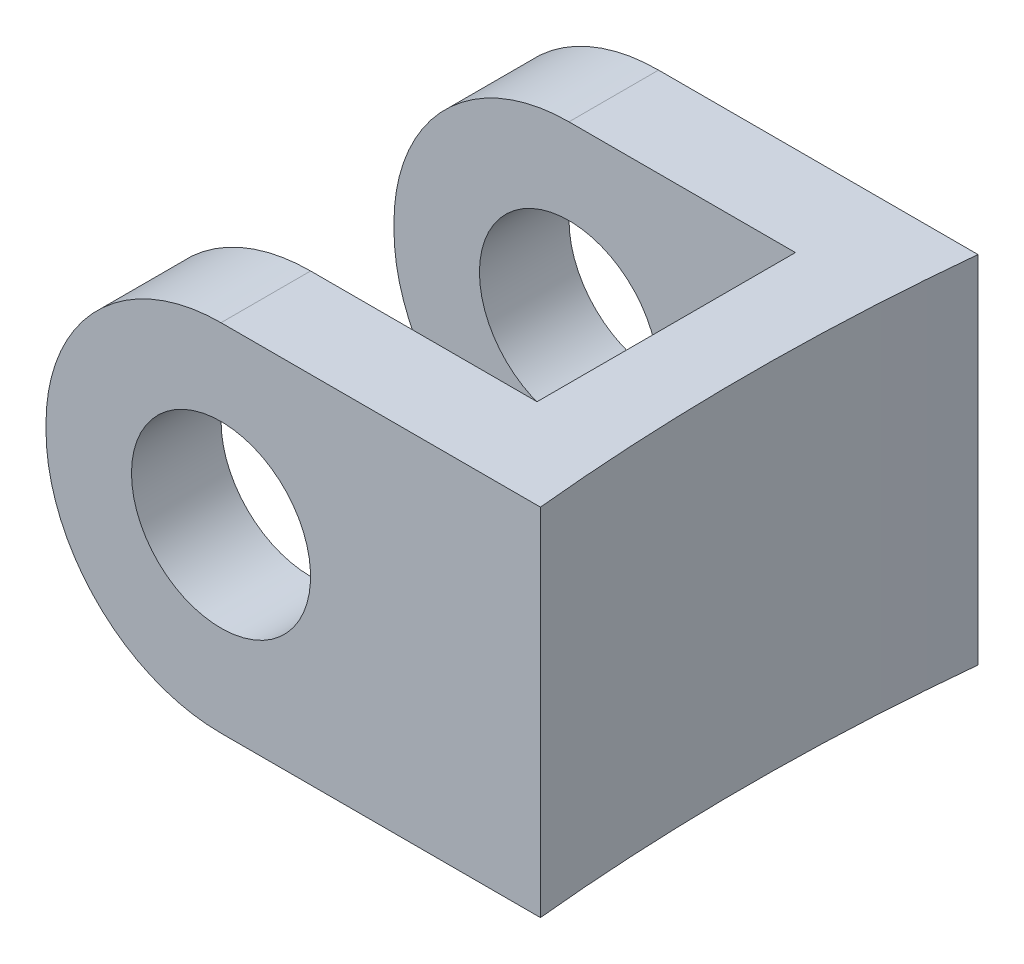
SolidWorks part; units mm, degrees
ref_plane "Front Plane" through (0, 0, 0) normal (0, 0, 1) x (1, 0, 0)
ref_plane "Top Plane" through (0, 0, 0) normal (0, 1, 0) x (1, 0, 0)
ref_plane "Right Plane" through (0, 0, 0) normal (1, 0, 0) x (0, 0, -1)
sketch "Sketch1" plane through (0, 0, 0) normal (0, 1, 0) x (1, 0, 0)
  line L0 (0, 0) -> (11.2268, 0)
  line L1 (0, 0) -> (0, -2.0803)
  line L4 (9.3218, -5.08) -> (9.3218, -2.0803)
  line L5 (9.3218, -2.0803) -> (0, -2.0803)
  line L6 (0, -8.0797) -> (0, -10.16)
  line L7 (9.3218, -5.08) -> (9.3218, -8.0797)
  line L8 (9.3218, -8.0797) -> (0, -8.0797)
  line L9 (0, -10.16) -> (11.2268, -10.16)
  line L12 (11.2268, -10.16) -> (11.4814, -10.16)
  line L13 (11.2268, 0) -> (11.4814, 0)
  arc A0 (11.4814, 0) -> (11.4814, -10.16) centre (62.0268, -5.08) ccw
  dimension "D1" = 11.2268
  dimension "D2" = 10.16
extrude "Boss-Extrude2" add sketch "Sketch1" along normal blind 8.255
fillet "Fillet1" radius 4.064 4 edges at (0, 0, 9.1199) (0, 8.255, 9.1199) (0, 0, 1.0401) (0, 8.255, 1.0401)
sketch "Sketch2" plane through (0, 0, 0) normal (0, 0, -1) x (-1, 0, 0)
  circle A0 centre (-4.064, 4.191) radius 2.079
  dimension "D2" = 4.158
extrude "Cut-Extrude1" cut sketch "Sketch2" against normal through all
